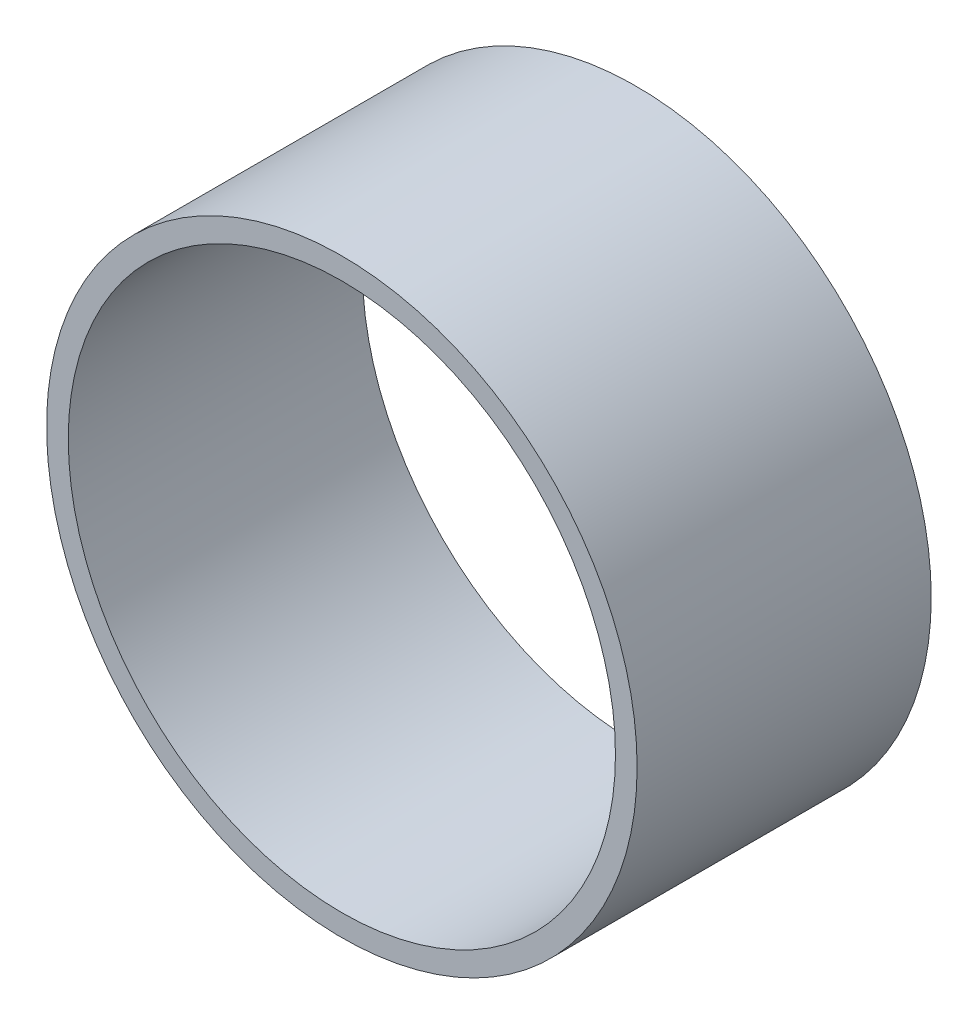
SolidWorks part; units mm, degrees
material "1023 炭素鋼板 (SS)"
ref_plane "正面" through (0, 0, 0) normal (0, 0, 1) x (1, 0, 0)
ref_plane "平面" through (0, 0, 0) normal (0, 1, 0) x (1, 0, 0)
ref_plane "右側面" through (0, 0, 0) normal (1, 0, 0) x (0, 0, -1)
sketch "ｽｹｯﾁ1" plane through (0, 0, 0) normal (0, 0, 1) x (1, 0, 0)
  circle A0 centre (0, 0) radius 38.15
  circle A1 centre (0, 0) radius 35.35
  dimension "D1" = 76.3
  dimension "D2" = 2.8
extrude "ﾎﾞｽ - 押し出し1" add sketch "ｽｹｯﾁ1" along normal blind 38
